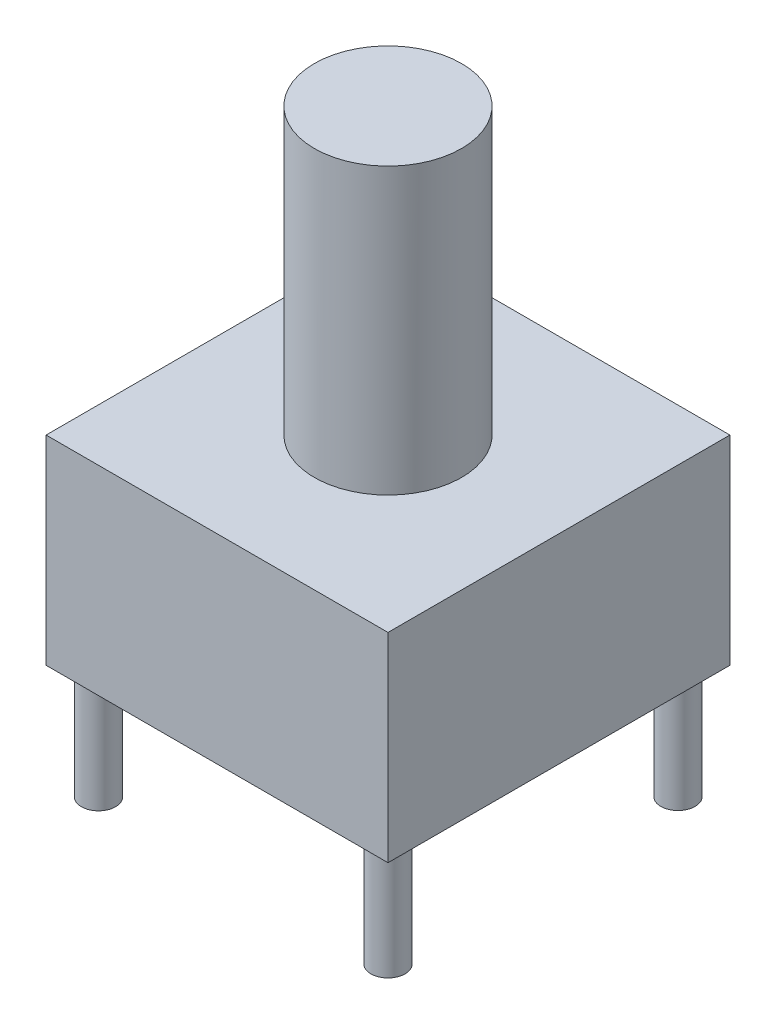
SolidWorks part; units mm, degrees
ref_plane "Спереди" through (0, 0, 0) normal (0, 0, 1) x (1, 0, 0)
ref_plane "Сверху" through (0, 0, 0) normal (0, 1, 0) x (1, 0, 0)
ref_plane "Справа" through (0, 0, 0) normal (1, 0, 0) x (0, 0, -1)
sketch "Sketch1" plane through (0, 0, 0) normal (0, 1, 0) x (1, 0, 0)
  line L1 (0, 0) -> (6, 0)
  line L2 (0, 0) -> (0, 6)
  line L3 (0, 6) -> (6, 6)
  line L4 (6, 0) -> (6, 6)
  dimension "D1" = 6
  dimension "D2" = 6
extrude "Boss-Extrude1" add sketch "Sketch1" along normal blind 3.5
sketch "Sketch2" plane through (0, 3.5, 0) normal (0, 1, 0) x (1, 0, 0)
  line L0 (0, 0) -> (6, 0) construction
  line L1 (0, 6) -> (0, 0) construction
  circle A0 centre (2.9993, 3) radius 1.2921
  point P6 (1.4113, 4.2031)
  point P7 (1.4234, 2.9861)
  dimension "D1" = 3
  dimension "D2" = 2.9993
extrude "Boss-Extrude2" add sketch "Sketch2" along normal blind 5
sketch "Sketch3" plane through (0, 0, 0) normal (0, -1, 0) x (-1, 0, 0)
  line L0 (0, 6) -> (0, 0) construction
  line L1 (-6, 6) -> (0, 6) construction
  circle A0 centre (-0.46, 0.46) radius 0.3
  circle A1 centre (-5.54, 0.46) radius 0.3
  circle A2 centre (-0.46, 5.54) radius 0.3
  circle A3 centre (-5.54, 5.5489) radius 0.3
  point P8 (-3, 3)
  point P13 (-3.4981, 3.6535)
  point P14 (0, 0)
  point P15 (0, 0)
  point P16 (0, 0)
  dimension "D1" = 5.08
  dimension "D2" = 5.08
  dimension "D3" = 3
  dimension "D4" = 3
  dimension "D5" = 2.54
  dimension "D6" = 2.54
  dimension "D7" = 5.08
extrude "Boss-Extrude3" add sketch "Sketch3" along normal blind 2
